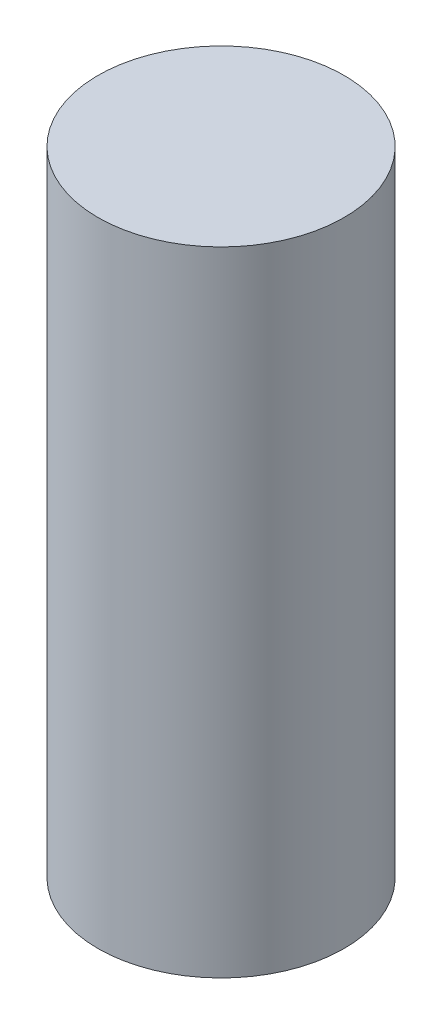
SolidWorks part; units mm, degrees
ref_plane "Front Plane" through (0, 0, 0) normal (0, 0, 1) x (1, 0, 0)
ref_plane "Top Plane" through (0, 0, 0) normal (0, 1, 0) x (1, 0, 0)
ref_plane "Right Plane" through (0, 0, 0) normal (1, 0, 0) x (0, 0, -1)
sketch "Sketch1" plane through (0, 0, 0) normal (0, 1, 0) x (1, 0, 0)
  circle A0 centre (0, 0) radius 1.75
  dimension "D1" = 3.5
extrude "Boss-Extrude1" add sketch "Sketch1" along normal blind 9
